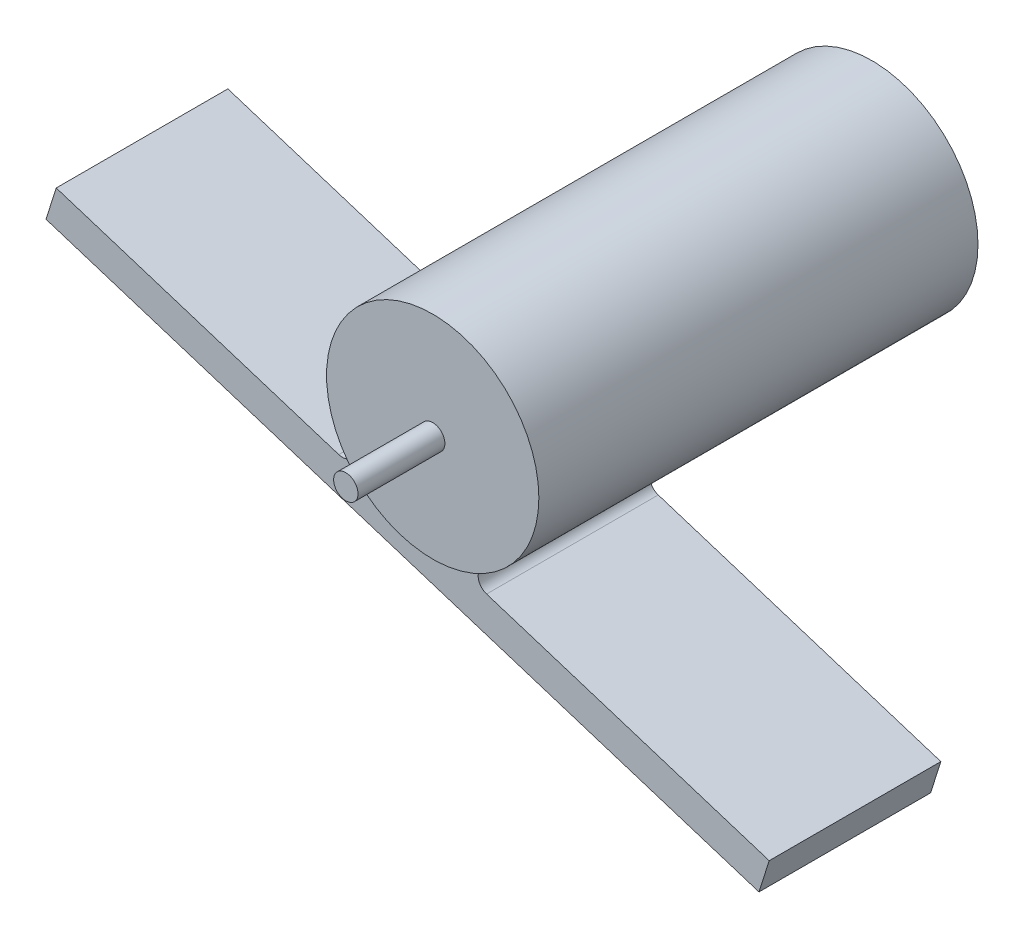
SolidWorks part; units mm, degrees
ref_plane "Front Plane" through (0, 0, 0) normal (0, 0, 1) x (1, 0, 0)
ref_plane "Top Plane" through (0, 0, 0) normal (0, 1, 0) x (1, 0, 0)
ref_plane "Right Plane" through (0, 0, 0) normal (1, 0, 0) x (0, 0, -1)
sketch "Sketch1" plane through (0, 0, 0) normal (0, 0, 1) x (1, 0, 0)
  circle A0 centre (-5.4927, -4.8388) radius 22
extrude "Boss-Extrude1" add sketch "Sketch1" along normal blind 91
sketch "Sketch2" plane through (0, 0, 91) normal (0, 0, 1) x (1, 0, 0)
  circle A0 centre (-5.4927, -4.8388) radius 2.5251
extrude "Boss-Extrude2" add sketch "Sketch2" along normal blind 18
sketch "Sketch3" plane through (0, 0, 91) normal (0, 0, 1) x (1, 0, 0)
  line L0 (-5.4927, -4.8388) -> (-12.143, -25.8096) construction
  circle A0 centre (-5.4927, -4.8388) radius 22 construction
ref_plane "Holder" through (-12.143, -25.8096, 91) normal (-0.3023, -0.9532, 0) x (-0.9532, 0.3023, 0)
sketch "Sketch4" plane through (-12.143, -25.8096, 91) normal (-0.3023, -0.9532, 0) x (-0.9532, 0.3023, 0)
  line L1 (-77.5, 37.7732) -> (77.5, 37.7732)
  line L2 (-77.5, 37.7732) -> (-77.5, 2.2033)
  line L3 (-77.5, 2.2033) -> (77.5, 2.2033)
  line L4 (77.5, 37.7732) -> (77.5, 2.2033)
  point P4 (0, 37.7732)
  dimension "D1" = 155
extrude "Boss-Extrude3" add sketch "Sketch4" against normal blind 1 and the other way blind 6
fillet "Fillet1" radius 2.5 1 edges at (-5.59, -26.8386, 71.0117)
fillet "Fillet2" radius 2.5 1 edges at (-18.0914, -22.8742, 71.0117)
